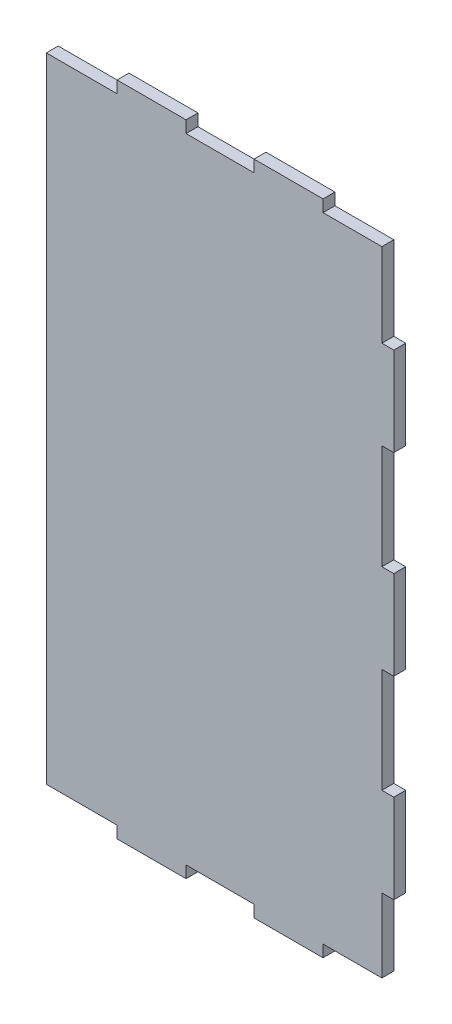
SolidWorks part; units mm, degrees
material "Maple"
ref_plane "Front Plane" through (0, 0, 0) normal (0, 0, 1) x (1, 0, 0)
ref_plane "Top Plane" through (0, 0, 0) normal (0, 1, 0) x (1, 0, 0)
ref_plane "Right Plane" through (0, 0, 0) normal (1, 0, 0) x (0, 0, -1)
sketch "Sketch1" plane through (0, 0, 0) normal (0, 0, 1) x (1, 0, 0)
  line L0 (0, -337) -> (350, -337) construction
  line L1 (71.25, 0) -> (140.75, 0)
  line L2 (0, -12) -> (0, -650)
  line L3 (71.25, -662) -> (140.75, -662)
  line L5 (350, -486.25) -> (350, -575.75)
  line L6 (350, -96.25) -> (338, -96.25)
  line L7 (338, -380.75) -> (350, -380.75)
  line L9 (338, -291.25) -> (350, -291.25)
  line L10 (350, -380.75) -> (350, -291.25)
  line L11 (350, -96.25) -> (350, -185.75)
  line L12 (350, -185.75) -> (338, -185.75)
  line L14 (350, -486.25) -> (338, -486.25)
  line L15 (350, -486.25) -> (350, -575.75)
  line L16 (350, -575.75) -> (338, -575.75)
  line L17 (338, -96.25) -> (338, -12)
  line L18 (338, -185.75) -> (338, -291.25)
  line L19 (338, -380.75) -> (338, -486.25)
  line L20 (338, -575.75) -> (338, -650)
  line L21 (71.25, -12) -> (0, -12)
  line L22 (71.25, 0) -> (140.75, 0)
  line L23 (71.25, 0) -> (71.25, -12)
  line L25 (140.75, 0) -> (140.75, -12)
  line L26 (209.25, 0) -> (278.75, 0)
  line L27 (209.25, 0) -> (209.25, -12)
  line L29 (278.75, 0) -> (278.75, -12)
  line L30 (140.75, -12) -> (209.25, -12)
  line L31 (278.75, -12) -> (338, -12)
  line L32 (209.25, 0) -> (278.75, 0)
  line L34 (209.25, -662) -> (278.75, -662)
  line L35 (278.75, -650) -> (338, -650)
  line L36 (140.75, -650) -> (209.25, -650)
  line L37 (278.75, -662) -> (278.75, -650)
  line L38 (209.25, -662) -> (209.25, -650)
  line L39 (209.25, -662) -> (278.75, -662)
  line L40 (140.75, -662) -> (140.75, -650)
  line L41 (71.25, -662) -> (71.25, -650)
  line L42 (71.25, -662) -> (140.75, -662)
  line L43 (71.25, -650) -> (0, -650)
  line L44 (71.25, -662) -> (140.75, -662)
  line L45 (209.25, -662) -> (278.75, -662)
  dimension "D2" = 12
  dimension "D3" = 89.5
  dimension "D4" = 12
  dimension "D5" = 89.5
  dimension "D6" = 86.25
  dimension "D7" = 71.25
  dimension "D8" = 89.5
  dimension "D9" = 662
  dimension "D10" = 71.25
  dimension "D11" = 69.5
  dimension "D12" = 71.25
  dimension "D13" = 69.5
  dimension "D14" = 68.5
  dimension "D15" = 12
  dimension "D16" = 69.5
  dimension "D17" = 71.25
  dimension "D18" = 69.5
  dimension "D19" = 105.5
  dimension "D20" = 105.5
extrude "Boss-Extrude1" add sketch "Sketch1" along normal blind 12 contours L0 L2 L43 L41 L3 L40 L36 L38 L34 L37 L35 L20 L16 L5 L14 L19 L7 L10 | L2 L0 L10 L9 L18 L12 L11 L6 L17 L31 L29 L26 L27 L30 L25 L1 L23 L21
